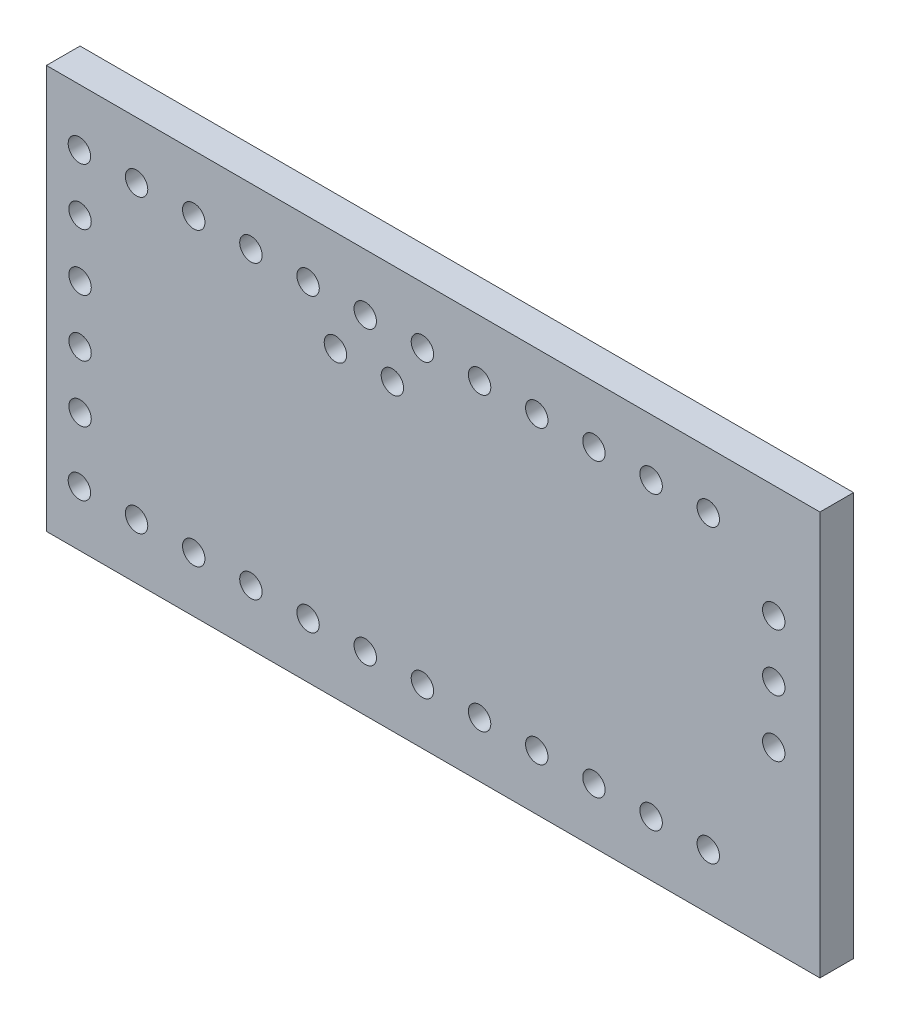
SolidWorks part; units mm, degrees
ref_plane "Alzado" through (0, 0, 0) normal (0, 0, 1) x (1, 0, 0)
ref_plane "Planta" through (0, 0, 0) normal (0, 1, 0) x (1, 0, 0)
ref_plane "Vista lateral" through (0, 0, 0) normal (1, 0, 0) x (0, 0, -1)
sketch "Croquis2" plane through (0, 0, 0) normal (0, 0, 1) x (1, 0, 0)
  line L1 (0, 0) -> (34.5, 0)
  line L2 (0, 0) -> (0, 18)
  line L3 (0, 18) -> (34.5, 18)
  line L4 (34.5, 0) -> (34.5, 18)
extrude "Saliente-Extruir1" add sketch "Croquis2" along normal blind 1.5
sketch "Croquis3" plane through (0, 0, 1.5) normal (0, 0, 1) x (1, 0, 0)
  circle A0 centre (4.02, 2.47) radius 0.5
  circle A1 centre (1.47, 2.47) radius 0.5
  circle A2 centre (1.5, 12.96) radius 0.5
  circle A3 centre (1.5, 10.42) radius 0.5
  circle A4 centre (1.5, 7.88) radius 0.5
  circle A5 centre (1.5, 5.34) radius 0.5
  circle A6 centre (6.57, 2.47) radius 0.5
  circle A7 centre (9.12, 2.47) radius 0.5
  circle A8 centre (11.67, 2.47) radius 0.5
  circle A9 centre (14.22, 2.47) radius 0.5
  circle A10 centre (16.77, 2.47) radius 0.5
  circle A11 centre (19.32, 2.47) radius 0.5
  circle A12 centre (21.87, 2.47) radius 0.5
  circle A13 centre (24.42, 2.47) radius 0.5
  circle A14 centre (26.97, 2.47) radius 0.5
  circle A16 centre (29.52, 2.47) radius 0.5
  circle A17 centre (4.02, 15.47) radius 0.5
  circle A18 centre (6.57, 15.47) radius 0.5
  circle A19 centre (9.12, 15.47) radius 0.5
  circle A20 centre (11.67, 15.47) radius 0.5
  circle A21 centre (14.22, 15.47) radius 0.5
  circle A22 centre (16.77, 15.47) radius 0.5
  circle A23 centre (19.32, 15.47) radius 0.5
  circle A24 centre (21.87, 15.47) radius 0.5
  circle A25 centre (24.42, 15.47) radius 0.5
  circle A26 centre (26.97, 15.47) radius 0.5
  circle A27 centre (29.52, 15.47) radius 0.5
  circle A28 centre (1.47, 15.47) radius 0.5
  circle A30 centre (32.44, 12.96) radius 0.5
  circle A31 centre (32.44, 10.42) radius 0.5
  circle A32 centre (32.44, 7.88) radius 0.5
  circle A33 centre (15.43, 13.5) radius 0.5
  circle A34 centre (12.89, 13.5) radius 0.5
  dimension "D1" = 12
  dimension "D2" = 2
extrude "Cortar-Extruir1" cut sketch "Croquis3" against normal up to next (1.5 mm away)
